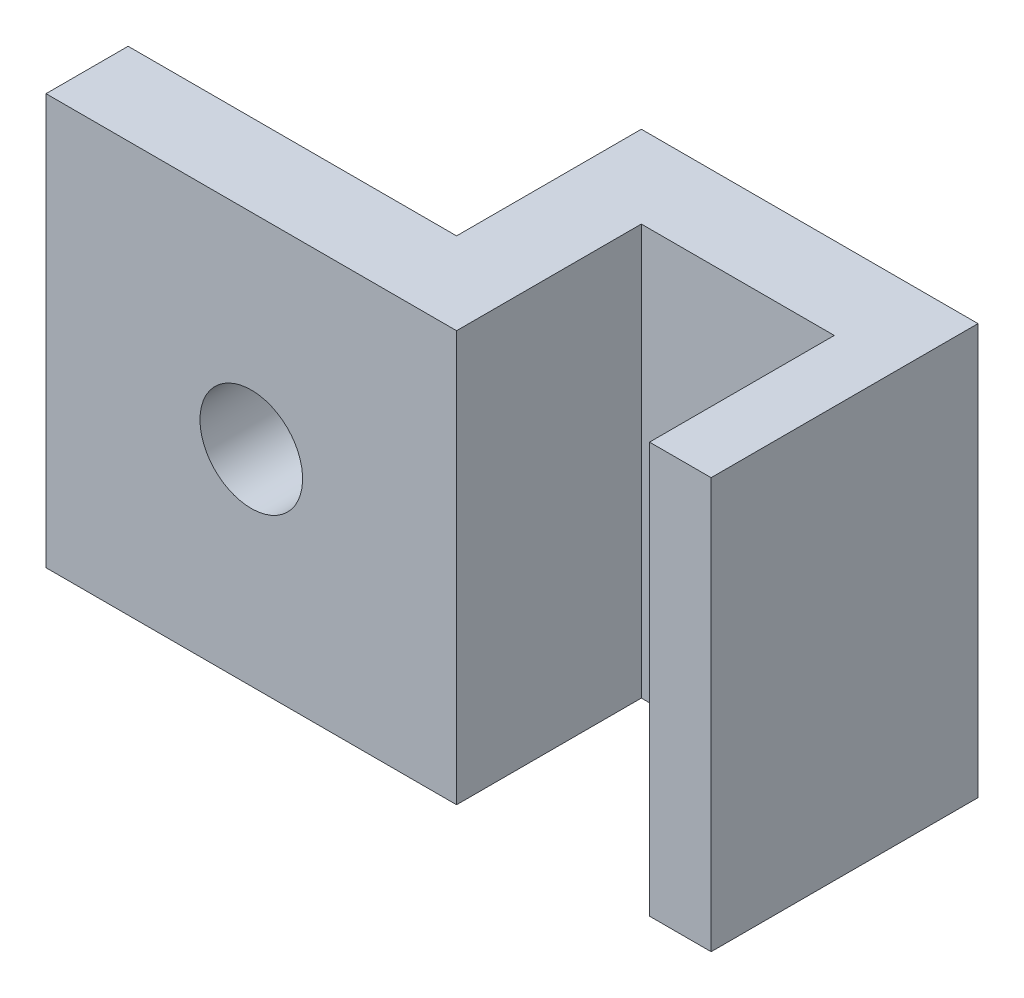
SolidWorks part; units mm, degrees
ref_plane "Alzado" through (0, 0, 0) normal (0, 0, 1) x (1, 0, 0)
ref_plane "Planta" through (0, 0, 0) normal (0, 1, 0) x (1, 0, 0)
ref_plane "Vista lateral" through (0, 0, 0) normal (1, 0, 0) x (0, 0, -1)
sketch "Croquis1" plane through (0, 0, 0) normal (0, 1, 0) x (1, 0, 0)
  line L0 (0, 0) -> (8, 0)
  line L1 (8, 0) -> (8, 4.5)
  line L2 (8, 4.5) -> (12.7, 4.5)
  line L3 (12.7, 4.5) -> (12.7, 0)
  line L4 (12.7, 0) -> (14.2, 0)
  line L5 (14.2, 0) -> (14.2, 6.5)
  line L6 (14.2, 6.5) -> (6, 6.5)
  line L7 (6, 6.5) -> (6, 2)
  line L8 (6, 2) -> (0, 2)
  line L9 (0, 2) -> (0, 0)
  dimension "D1" = 4.7
  dimension "D2" = 1.5
  dimension "D3" = 4.5
  dimension "D4" = 2
  dimension "D5" = 2
  dimension "D6" = 6
  dimension "D7" = 2
extrude "Saliente-Extruir1" add sketch "Croquis1" along normal blind 10
sketch "Croquis2" plane through (0, 0, -2) normal (0, 0, -1) x (-1, 0, 0)
  line L0 (-6, 0) -> (0, 10) construction
  line L1 (0, 10) -> (0, 0) construction
  line L2 (0, 0) -> (-6, 10) construction
  circle A0 centre (-3, 5) radius 1.25
  dimension "D1" = 2.5
extrude "Cortar-Extruir1" cut sketch "Croquis2" against normal blind 10
sketch "Croquis3" plane through (0, 0, 0) normal (-1, 0, 0) x (0, 0, 1)
  line L1 (0, 0) -> (-2, 0)
  line L2 (0, 0) -> (0, 10)
  line L3 (0, 10) -> (-2, 10)
  line L4 (-2, 0) -> (-2, 10)
extrude "Saliente-Extruir2" add sketch "Croquis3" along normal blind 2
